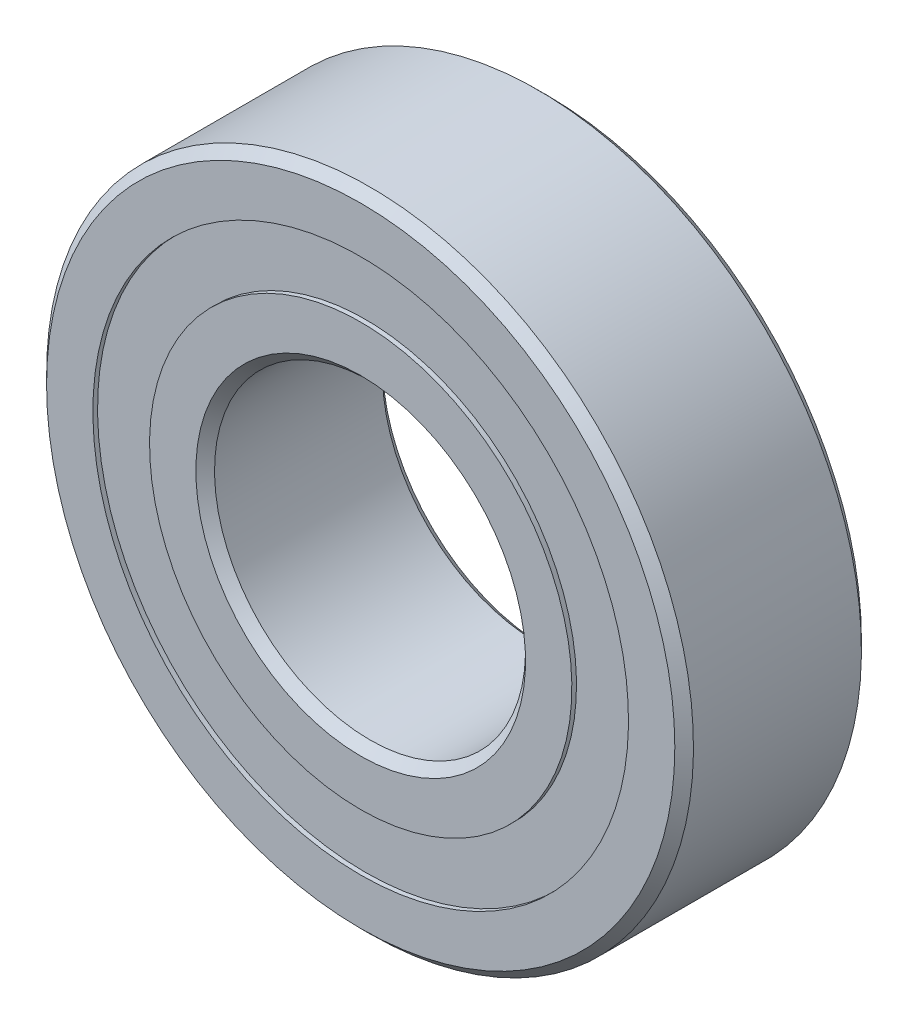
SolidWorks part; units mm, degrees
ref_plane "Front Plane" through (0, 0, 0) normal (0, 0, 1) x (1, 0, 0)
ref_plane "Top Plane" through (0, 0, 0) normal (0, 1, 0) x (1, 0, 0)
ref_plane "Right Plane" through (0, 0, 0) normal (1, 0, 0) x (0, 0, -1)
sketch "Sketch1" plane through (0, 0, 0) normal (0, 0, 1) x (1, 0, 0)
  line L0 (-26, 0) -> (26, 0) construction
  line L1 (-12.5, 0) -> (12.5, 0) construction
  circle A0 centre (0, 0) radius 12.5 construction
  circle A1 centre (0, 0) radius 26 construction
  point P3 (0, 0)
  point P6 (0, 0)
  point P7 (0, -12.5)
  point P11 (0, -26)
  point P12 (0, 12.5)
  point P13 (0, 26)
  dimension "OD" = 52
  dimension "ID" = 25
sketch "SketchB" plane through (0, 0, 0) normal (1, 0, 0) x (0, 0, -1)
  line L0 (-7.5, 26) -> (7.5, 26) construction
  line L1 (0, 26) -> (0, -26) construction
  line L2 (6.75, 26) -> (-6.75, 26)
  line L3 (-6.75, 26) -> (-7.5, 25.25)
  line L4 (-7.5, 25.25) -> (-7.5, 21.5269)
  line L5 (-7.5, 21.5269) -> (-3.3333, 21.5269)
  line L6 (7.5, 21.5269) -> (3.3333, 21.5269)
  line L7 (7.5, 25.25) -> (7.5, 21.5269)
  line L8 (6.75, 26) -> (7.5, 25.25)
  line L9 (0, 26) -> (0, 19.25) construction
  line L10 (0, 19.25) -> (0, 12.5) construction
  line L11 (0, 26) -> (0, -26) construction
  line L12 (-7.5, 0) -> (7.5, 0) construction
  line L13 (7.5, 12.5) -> (-7.5, 12.5) construction
  line L15 (-7.5, -12.5) -> (7.5, -12.5) construction
  arc A0 (-3.3333, 21.5269) -> (3.3333, 21.5269) centre (0, 19.25) cw
  circle A1 centre (0, 19.25) radius 4.0368 construction
  point P14 (0, 12.5)
  point P17 (0, 0)
  point P21 (0, 26)
  point P29 (0, 12.5)
  point P30 (0, -12.5)
  dimension "Width" = 15
  dimension "D1" = 45
  dimension "D2" = 0.75
  dimension "D3" = 6.6667
  dimension "D4" = 2.2769
sketch "Sketch7" plane through (0, 0, 0) normal (1, 0, 0) x (0, 0, -1)
  line L0 (6.75, 26) -> (7.5, 25.25) construction
  line L1 (7.5, 25.25) -> (7.5, 21.5269) construction
  line L2 (7.5, 21.5269) -> (3.3333, 21.5269) construction
  line L3 (-7.5, 21.5269) -> (-3.3333, 21.5269) construction
  line L4 (-7.5, 25.25) -> (-7.5, 21.5269) construction
  line L5 (-6.75, 26) -> (-7.5, 25.25) construction
  line L6 (6.75, 26) -> (-6.75, 26) construction
  line L7 (6.75, 26) -> (7.5, 25.25)
  line L8 (7.5, 25.25) -> (7.5, 21.5269)
  line L9 (7.5, 21.5269) -> (3.3333, 21.5269)
  line L10 (-7.5, 21.5269) -> (-3.3333, 21.5269)
  line L11 (-7.5, 25.25) -> (-7.5, 21.5269)
  line L12 (-6.75, 26) -> (-7.5, 25.25)
  line L13 (6.75, 26) -> (-6.75, 26)
  arc A0 (3.3333, 21.5269) -> (-3.3333, 21.5269) centre (0, 19.25) ccw construction
  arc A1 (3.3333, 21.5269) -> (-3.3333, 21.5269) centre (0, 19.25) ccw
revolve "Revolve6" add sketch "Sketch7" angle 360 about L12
sketch "Sketch3" plane through (0, 0, 0) normal (1, 0, 0) x (0, 0, -1)
  line L0 (0, 26) -> (0, -26) construction
  line L1 (0, 26) -> (0, -26) construction
  line L2 (-6.75, 12.5) -> (-7.5, 13.25)
  line L3 (-7.5, 13.25) -> (-7.5, 16.9731)
  line L5 (-7.5, 16.9731) -> (-3.3333, 16.9731)
  line L6 (-6.75, 12.5) -> (6.75, 12.5)
  line L8 (6.75, 12.5) -> (7.5, 13.25)
  line L10 (7.5, 13.25) -> (7.5, 16.9731)
  line L11 (7.5, 16.9731) -> (3.3333, 16.9731)
  line L12 (-7.5, 25.25) -> (-7.5, 21.5269) construction
  line L13 (6.75, 26) -> (7.5, 25.25) construction
  line L15 (7.5, -25.25) -> (7.5, 25.25) construction
  line L16 (6.75, 26) -> (6.75, -26) construction
  arc A1 (3.3333, 16.9731) -> (-3.3333, 16.9731) centre (0, 19.25) cw
  circle A2 centre (0, 19.25) radius 4.0368 construction
  point P1 (0, 12.5)
revolve "Revolve3" add sketch "Sketch3" angle 360 about L12
sketch "Sketch4" plane through (0, 0, 0) normal (1, 0, 0) x (0, 0, -1)
  line L0 (-4.0368, 19.25) -> (4.0368, 19.25)
  arc A2 (-4.0368, 19.25) -> (4.0368, 19.25) centre (0, 19.25) cw
  arc A3 (3.3333, 21.5269) -> (-3.3333, 21.5269) centre (0, 19.25) ccw construction
revolve "Revolve4" add sketch "Sketch4" angle 360 about L0
pattern_circular "CirPattern1" count 9 over 360 about axis through (0, 0, 0) along (0, 0, 1) of bodies 104
sketch "Sketch5" plane through (0, 0, 0) normal (1, 0, 0) x (0, 0, -1)
  line L0 (-7.5, 21.5269) -> (-3.3333, 21.5269) construction
  line L1 (-7.125, 21.5269) -> (-4.0368, 21.5269)
  line L2 (-7.125, 21.5269) -> (-7.125, 16.9731)
  line L3 (-7.125, 16.9731) -> (-4.0368, 16.9731)
  line L4 (-4.0368, 21.5269) -> (-4.0368, 16.9731)
  line L5 (-7.5, 16.9731) -> (-3.3333, 16.9731) construction
  line L6 (-6.75, 26) -> (-7.5, 25.25) construction
  line L7 (0, 26) -> (0, 12.5) construction
  line L8 (7.125, 16.9731) -> (4.0368, 16.9731)
  line L9 (4.0368, 21.5269) -> (4.0368, 16.9731)
  line L10 (7.125, 21.5269) -> (4.0368, 21.5269)
  line L11 (7.125, 21.5269) -> (7.125, 16.9731)
  circle A1 centre (0, 19.25) radius 4.0368 construction
  point P10 (-7.125, 25.625)
revolve "Revolve5" add sketch "Sketch5" angle 360 about L12
equation "\"D2@SketchB\" = \"Width@SketchB\" * .05"
equation "\"D3@SketchB\" = \"Width@SketchB\" / 2.25"
equation "\"D4@SketchB\" =  (  (  ( \"OD@Sketch1\" - \"Width@SketchB\" )  / 2 )  / 3.25 )  / 2.5"
